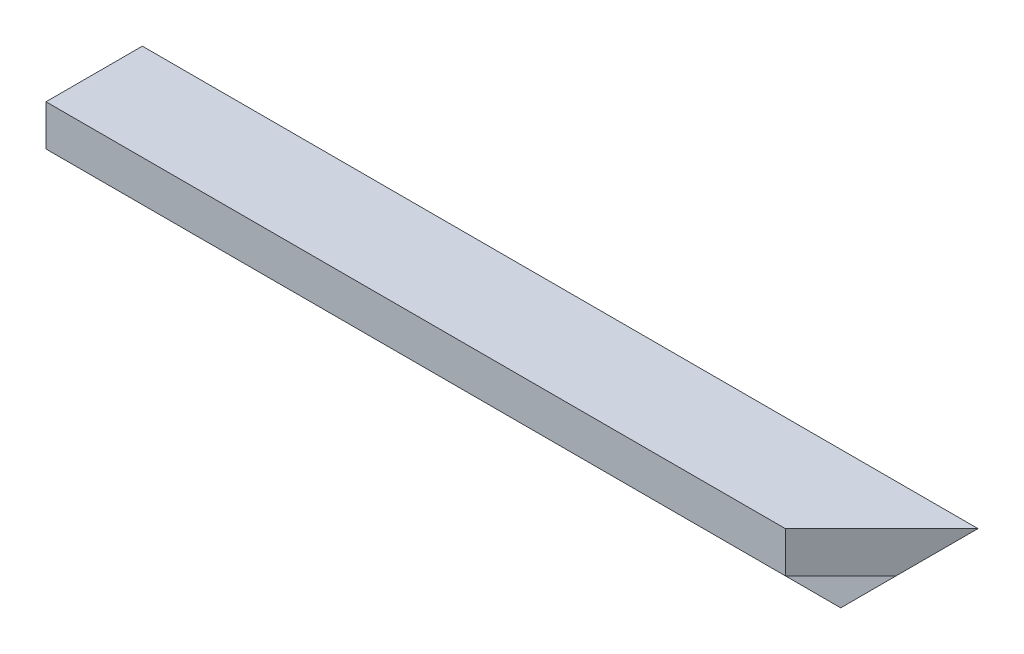
SolidWorks part; units mm, degrees
ref_plane "Plan de face" through (0, 0, 0) normal (0, 0, 1) x (1, 0, 0)
ref_plane "Plan de dessus" through (0, 0, 0) normal (0, 1, 0) x (1, 0, 0)
ref_plane "Plan de droite" through (0, 0, 0) normal (1, 0, 0) x (0, 0, -1)
sketch "Esquisse1" plane through (0, 0, 0) normal (1, 0, 0) x (0, 0, -1)
  line L0 (0, 0) -> (-40, 0)
  line L1 (-40, 0) -> (-40, -17)
  line L2 (-40, -17) -> (-17, -17)
  line L3 (-17, -17) -> (-17, -40)
  line L4 (-17, -40) -> (0, -40)
  line L5 (0, -40) -> (0, 0)
  dimension "D1" = 40
  dimension "D2" = 17
extrude "Boss.-Extru.1" add sketch "Esquisse1" against normal up to vertex (347 mm away)
sketch "Esquisse2" plane through (0, 0, 0) normal (0, 1, 0) x (1, 0, 0)
  line L0 (0, 0) -> (0, -40)
  line L2 (0, -40) -> (-40, -40)
  line L3 (-40, -40) -> (0, 0)
  line L5 (-347, -40) -> (0, -40) construction
  line L6 (-347, 0) -> (0, 0) construction
  point P2 (-150.9747, -40)
  point P3 (-89.0612, -40)
  point P5 (0, 0)
  point P7 (-43.4829, -40)
  point P12 (6.2431, -40)
  point P15 (0, 0)
  point P16 (0, -40)
  point P18 (-40.2088, 0)
  point P21 (0, 0)
extrude "Enlèv. mat.-Extru.1" cut sketch "Esquisse2" against normal through all
sketch "Esquisse3" plane through (0, 0, 0) normal (0, 0, -1) x (-1, 0, 0)
  line L4 (0, -40) -> (0, 0)
  line L5 (0, 0) -> (40, -40)
  line L6 (347, -40) -> (0, -40) construction
  line L7 (40, -40) -> (0, -40)
extrude "Enlèv. mat.-Extru.2" cut sketch "Esquisse3" against normal through all
